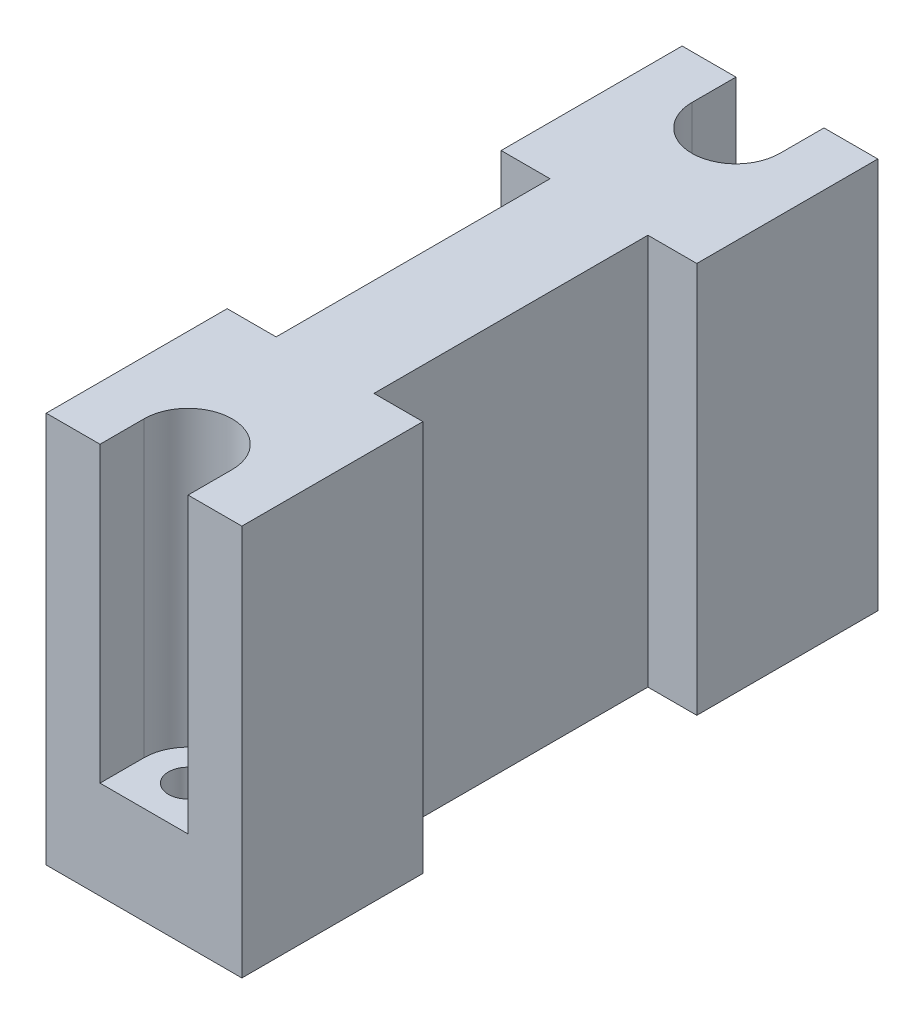
SolidWorks part; units mm, degrees
ref_plane "Front Plane" through (0, 0, 0) normal (0, 0, 1) x (1, 0, 0)
ref_plane "Top Plane" through (0, 0, 0) normal (0, 1, 0) x (1, 0, 0)
ref_plane "Right Plane" through (0, 0, 0) normal (1, 0, 0) x (0, 0, -1)
sketch "Sketch1" plane through (0, 0, 0) normal (0, 1, 0) x (1, 0, 0)
  line L1 (0, 0) -> (20, 0)
  line L2 (0, 0) -> (0, 65)
  line L3 (0, 65) -> (20, 65)
  line L4 (20, 0) -> (20, 65)
  dimension "D1" = 20
  dimension "D2" = 65
extrude "Boss-Extrude1" add sketch "Sketch1" along normal blind 40
sketch "Sketch2" plane through (0, 40, 0) normal (0, 1, 0) x (1, 0, 0)
  line L0 (20, 0) -> (20, 65) construction
  line L1 (20, 18.5) -> (15, 18.5)
  line L2 (20, 18.5) -> (20, 46.5)
  line L3 (20, 46.5) -> (15, 46.5)
  line L4 (15, 18.5) -> (15, 46.5)
  line L5 (0, 65) -> (0, 0) construction
  line L6 (20, 65) -> (0, 65) construction
  line L7 (5, 18.5) -> (0, 18.5)
  line L8 (5, 18.5) -> (5, 46.5)
  line L9 (5, 46.5) -> (0, 46.5)
  line L10 (0, 18.5) -> (0, 46.5)
  line L11 (0, 0) -> (20, 0) construction
  circle A0 centre (10, 60.5) radius 2
  circle A1 centre (10, 4.5) radius 2
  point P6 (15, 32.5)
  point P9 (0, 32.5)
  dimension "D5" = 4
  dimension "D7" = 4
  dimension "D1" = 28
  dimension "D2" = 0
  dimension "D3" = 5
  dimension "D4" = 5
  dimension "D6" = 4.5
  dimension "D8" = 4.5
extrude "Cut-Extrude1" cut sketch "Sketch2" against normal blind 40
sketch "Sketch4" plane through (0, 40, 0) normal (0, 1, 0) x (1, 0, 0)
  line L0 (0, 0) -> (20, 0) construction
  line L1 (5.5, 4.5) -> (14.5, 4.5)
  line L2 (5.5, 4.5) -> (5.5, 0)
  line L3 (5.5, 0) -> (14.5, 0)
  line L4 (14.5, 4.5) -> (14.5, 0)
  line L5 (20, 65) -> (0, 65) construction
  line L6 (5.5, 60.5) -> (14.5, 60.5)
  line L7 (5.5, 60.5) -> (5.5, 65)
  line L8 (5.5, 65) -> (14.5, 65)
  line L9 (14.5, 60.5) -> (14.5, 65)
  circle A0 centre (10, 4.5) radius 4.5
  circle A1 centre (10, 60.5) radius 4.5
extrude "Cut-Extrude4" cut sketch "Sketch4" against normal blind 30 contours L7 L8 L9 L6 | A1 | L2 L3 L4 L1 | A0
